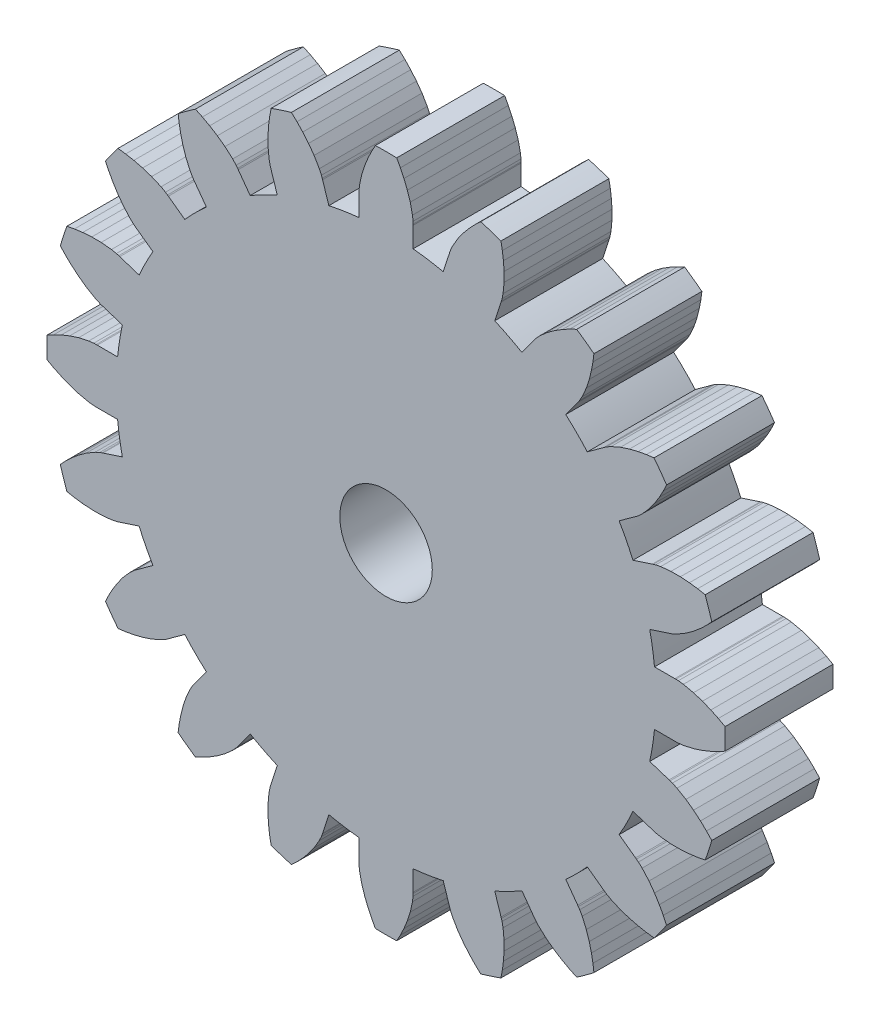
SolidWorks part; units mm, degrees
ref_plane "Front Plane" through (0, 0, 0) normal (0, 0, 1) x (1, 0, 0)
ref_plane "Top Plane" through (0, 0, 0) normal (0, 1, 0) x (1, 0, 0)
ref_plane "Right Plane" through (0, 0, 0) normal (1, 0, 0) x (0, 0, -1)
ref_plane "Plan1" through (0, 0, 10) normal (0, 0, 1) x (1, 0, 0)
sketch "Esquisse1" plane through (0, 0, 10) normal (0, 0, 1) x (1, 0, 0)
  line L0 (10.3919, 2.8876) -> (10.5632, 3.069)
  line L1 (10.3497, 3.726) -> (10.1045, 3.7722)
  line L2 (10.1045, 3.7722) -> (9.8372, 3.8071)
  line L3 (9.8372, 3.8071) -> (9.5442, 3.8279)
  line L4 (9.5442, 3.8279) -> (9.2385, 3.8276)
  line L5 (9.2385, 3.8276) -> (8.9055, 3.7951)
  line L6 (8.9055, 3.7951) -> (8.7443, 3.7625)
  line L7 (8.7443, 3.7625) -> (8.6676, 3.7409)
  line L8 (8.6676, 3.7409) -> (8.6349, 3.7295)
  line L9 (8.6349, 3.7295) -> (8.0083, 3.5256)
  line L10 (7.5594, 4.4066) -> (8.0927, 4.7936)
  line L11 (8.0927, 4.7936) -> (8.1211, 4.8134)
  line L12 (8.1211, 4.8134) -> (8.1837, 4.8627)
  line L13 (8.1837, 4.8627) -> (8.3048, 4.974)
  line L14 (8.3048, 4.974) -> (8.5268, 5.2243)
  line L15 (8.5268, 5.2243) -> (8.7068, 5.4714)
  line L16 (8.7068, 5.4714) -> (8.8622, 5.7207)
  line L17 (8.8622, 5.7207) -> (8.991, 5.9575)
  line L18 (8.991, 5.9575) -> (9.0978, 6.183)
  line L19 (8.6918, 6.7419) -> (8.4443, 6.71)
  line L20 (8.4443, 6.71) -> (8.1793, 6.6606)
  line L21 (8.1793, 6.6606) -> (7.8942, 6.5899)
  line L22 (7.8942, 6.5899) -> (7.6035, 6.4951)
  line L23 (7.6035, 6.4951) -> (7.2969, 6.3613)
  line L24 (7.2969, 6.3613) -> (7.1536, 6.2805)
  line L25 (7.1536, 6.2805) -> (7.0874, 6.2362)
  line L26 (7.0874, 6.2362) -> (7.0598, 6.2153)
  line L27 (7.0598, 6.2153) -> (6.5269, 5.8277)
  line L28 (5.8277, 6.5269) -> (6.2153, 7.0598)
  line L29 (6.2153, 7.0598) -> (6.2362, 7.0874)
  line L30 (6.2362, 7.0874) -> (6.2805, 7.1536)
  line L31 (6.2805, 7.1536) -> (6.3613, 7.2969)
  line L32 (6.3613, 7.2969) -> (6.4951, 7.6035)
  line L33 (6.4951, 7.6035) -> (6.5899, 7.8942)
  line L34 (6.5899, 7.8942) -> (6.6606, 8.1793)
  line L35 (6.6606, 8.1793) -> (6.71, 8.4443)
  line L36 (6.71, 8.4443) -> (6.7419, 8.6918)
  line L37 (6.183, 9.0978) -> (5.9575, 8.991)
  line L38 (5.9575, 8.991) -> (5.7207, 8.8622)
  line L39 (5.7207, 8.8622) -> (5.4714, 8.7068)
  line L40 (5.4714, 8.7068) -> (5.2243, 8.5268)
  line L41 (5.2243, 8.5268) -> (4.974, 8.3048)
  line L42 (4.974, 8.3048) -> (4.8627, 8.1837)
  line L43 (4.8627, 8.1837) -> (4.8134, 8.1211)
  line L44 (4.8134, 8.1211) -> (4.7936, 8.0927)
  line L45 (4.7936, 8.0927) -> (4.4066, 7.5594)
  line L46 (3.5256, 8.0083) -> (3.7295, 8.6349)
  line L47 (3.7295, 8.6349) -> (3.7409, 8.6676)
  line L48 (3.7409, 8.6676) -> (3.7625, 8.7443)
  line L49 (3.7625, 8.7443) -> (3.7951, 8.9055)
  line L50 (3.7951, 8.9055) -> (3.8276, 9.2385)
  line L51 (3.8276, 9.2385) -> (3.8279, 9.5442)
  line L52 (3.8279, 9.5442) -> (3.8071, 9.8372)
  line L53 (3.8071, 9.8372) -> (3.7722, 10.1045)
  line L54 (3.7722, 10.1045) -> (3.726, 10.3497)
  line L55 (3.069, 10.5632) -> (2.8876, 10.3919)
  line L56 (2.8876, 10.3919) -> (2.7022, 10.1962)
  line L57 (2.7022, 10.1962) -> (2.5131, 9.9714)
  line L58 (2.5131, 9.9714) -> (2.3337, 9.7239)
  line L59 (2.3337, 9.7239) -> (2.1642, 9.4354)
  line L60 (2.1642, 9.4354) -> (2.0958, 9.2858)
  line L61 (2.0958, 9.2858) -> (2.0682, 9.211)
  line L62 (2.0682, 9.211) -> (2.0582, 9.1779)
  line L63 (2.0582, 9.1779) -> (1.8549, 8.5511)
  line L64 (0.8783, 8.7058) -> (0.8787, 9.3647)
  line L65 (0.8787, 9.3647) -> (0.8794, 9.3993)
  line L66 (0.8794, 9.3993) -> (0.8763, 9.479)
  line L67 (0.8763, 9.479) -> (0.8574, 9.6424)
  line L68 (0.8574, 9.6424) -> (0.7854, 9.9691)
  line L69 (0.7854, 9.9691) -> (0.6913, 10.26)
  line L70 (0.6913, 10.26) -> (0.5809, 10.5322)
  line L71 (0.5809, 10.5322) -> (0.4651, 10.7756)
  line L72 (0.4651, 10.7756) -> (0.3454, 10.9946)
  line L73 (-0.3454, 10.9946) -> (-0.4651, 10.7756)
  line L74 (-0.4651, 10.7756) -> (-0.5809, 10.5322)
  line L75 (-0.5809, 10.5322) -> (-0.6913, 10.26)
  line L76 (-0.6913, 10.26) -> (-0.7854, 9.9691)
  line L77 (-0.7854, 9.9691) -> (-0.8574, 9.6424)
  line L78 (-0.8574, 9.6424) -> (-0.8763, 9.479)
  line L79 (-0.8763, 9.479) -> (-0.8794, 9.3993)
  line L80 (-0.8794, 9.3993) -> (-0.8787, 9.3647)
  line L81 (-0.8787, 9.3647) -> (-0.8783, 8.7058)
  line L82 (-1.8549, 8.5511) -> (-2.0582, 9.1779)
  line L83 (-2.0582, 9.1779) -> (-2.0682, 9.211)
  line L84 (-2.0682, 9.211) -> (-2.0958, 9.2858)
  line L85 (-2.0958, 9.2858) -> (-2.1642, 9.4354)
  line L86 (-2.1642, 9.4354) -> (-2.3337, 9.7239)
  line L87 (-2.3337, 9.7239) -> (-2.5131, 9.9714)
  line L88 (-2.5131, 9.9714) -> (-2.7022, 10.1962)
  line L89 (-2.7022, 10.1962) -> (-2.8876, 10.3919)
  line L90 (-2.8876, 10.3919) -> (-3.069, 10.5632)
  line L91 (-3.726, 10.3497) -> (-3.7722, 10.1045)
  line L92 (-3.7722, 10.1045) -> (-3.8071, 9.8372)
  line L93 (-3.8071, 9.8372) -> (-3.8279, 9.5442)
  line L94 (-3.8279, 9.5442) -> (-3.8276, 9.2385)
  line L95 (-3.8276, 9.2385) -> (-3.7951, 8.9055)
  line L96 (-3.7951, 8.9055) -> (-3.7625, 8.7443)
  line L97 (-3.7625, 8.7443) -> (-3.7409, 8.6676)
  line L98 (-3.7409, 8.6676) -> (-3.7295, 8.6349)
  line L99 (-3.7295, 8.6349) -> (-3.5256, 8.0083)
  line L100 (-4.4066, 7.5594) -> (-4.7936, 8.0927)
  line L101 (-4.7936, 8.0927) -> (-4.8134, 8.1211)
  line L102 (-4.8134, 8.1211) -> (-4.8627, 8.1837)
  line L103 (-4.8627, 8.1837) -> (-4.974, 8.3048)
  line L104 (-4.974, 8.3048) -> (-5.2243, 8.5268)
  line L105 (-5.2243, 8.5268) -> (-5.4714, 8.7068)
  line L106 (-5.4714, 8.7068) -> (-5.7207, 8.8622)
  line L107 (-5.7207, 8.8622) -> (-5.9575, 8.991)
  line L108 (-5.9575, 8.991) -> (-6.183, 9.0978)
  line L109 (-6.7419, 8.6918) -> (-6.71, 8.4443)
  line L110 (-6.71, 8.4443) -> (-6.6606, 8.1793)
  line L111 (-6.6606, 8.1793) -> (-6.5899, 7.8942)
  line L112 (-6.5899, 7.8942) -> (-6.4951, 7.6035)
  line L113 (-6.4951, 7.6035) -> (-6.3613, 7.2969)
  line L114 (-6.3613, 7.2969) -> (-6.2805, 7.1536)
  line L115 (-6.2805, 7.1536) -> (-6.2362, 7.0874)
  line L116 (-6.2362, 7.0874) -> (-6.2153, 7.0598)
  line L117 (-6.2153, 7.0598) -> (-5.8277, 6.5269)
  line L118 (-6.5269, 5.8277) -> (-7.0598, 6.2153)
  line L119 (-7.0598, 6.2153) -> (-7.0874, 6.2362)
  line L120 (-7.0874, 6.2362) -> (-7.1536, 6.2805)
  line L121 (-7.1536, 6.2805) -> (-7.2969, 6.3613)
  line L122 (-7.2969, 6.3613) -> (-7.6035, 6.4951)
  line L123 (-7.6035, 6.4951) -> (-7.8942, 6.5899)
  line L124 (-7.8942, 6.5899) -> (-8.1793, 6.6606)
  line L125 (-8.1793, 6.6606) -> (-8.4443, 6.71)
  line L126 (-8.4443, 6.71) -> (-8.6918, 6.7419)
  line L127 (-9.0978, 6.183) -> (-8.991, 5.9575)
  line L128 (-8.991, 5.9575) -> (-8.8622, 5.7207)
  line L129 (-8.8622, 5.7207) -> (-8.7068, 5.4714)
  line L130 (-8.7068, 5.4714) -> (-8.5268, 5.2243)
  line L131 (-8.5268, 5.2243) -> (-8.3048, 4.974)
  line L132 (-8.3048, 4.974) -> (-8.1837, 4.8627)
  line L133 (-8.1837, 4.8627) -> (-8.1211, 4.8134)
  line L134 (-8.1211, 4.8134) -> (-8.0927, 4.7936)
  line L135 (-8.0927, 4.7936) -> (-7.5594, 4.4066)
  line L136 (-8.0083, 3.5256) -> (-8.6349, 3.7295)
  line L137 (-8.6349, 3.7295) -> (-8.6676, 3.7409)
  line L138 (-8.6676, 3.7409) -> (-8.7443, 3.7625)
  line L139 (-8.7443, 3.7625) -> (-8.9055, 3.7951)
  line L140 (-8.9055, 3.7951) -> (-9.2385, 3.8276)
  line L141 (-9.2385, 3.8276) -> (-9.5442, 3.8279)
  line L142 (-9.5442, 3.8279) -> (-9.8372, 3.8071)
  line L143 (-9.8372, 3.8071) -> (-10.1045, 3.7722)
  line L144 (-10.1045, 3.7722) -> (-10.3497, 3.726)
  line L145 (-10.5632, 3.069) -> (-10.3919, 2.8876)
  line L146 (-10.3919, 2.8876) -> (-10.1962, 2.7022)
  line L147 (-10.1962, 2.7022) -> (-9.9714, 2.5131)
  line L148 (-9.9714, 2.5131) -> (-9.7239, 2.3337)
  line L149 (-9.7239, 2.3337) -> (-9.4354, 2.1642)
  line L150 (-9.4354, 2.1642) -> (-9.2858, 2.0958)
  line L151 (-9.2858, 2.0958) -> (-9.211, 2.0682)
  line L152 (-9.211, 2.0682) -> (-9.1779, 2.0582)
  line L153 (-9.1779, 2.0582) -> (-8.5511, 1.8549)
  line L154 (-8.7058, 0.8783) -> (-9.3647, 0.8787)
  line L155 (-9.3647, 0.8787) -> (-9.3993, 0.8794)
  line L156 (-9.3993, 0.8794) -> (-9.479, 0.8763)
  line L157 (-9.479, 0.8763) -> (-9.6424, 0.8574)
  line L158 (-9.6424, 0.8574) -> (-9.9691, 0.7854)
  line L159 (-9.9691, 0.7854) -> (-10.26, 0.6913)
  line L160 (-10.26, 0.6913) -> (-10.5322, 0.5809)
  line L161 (-10.5322, 0.5809) -> (-10.7756, 0.4651)
  line L162 (-10.7756, 0.4651) -> (-10.9946, 0.3454)
  line L163 (-10.9946, -0.3454) -> (-10.7756, -0.4651)
  line L164 (-10.7756, -0.4651) -> (-10.5322, -0.5809)
  line L165 (-10.5322, -0.5809) -> (-10.26, -0.6913)
  line L166 (-10.26, -0.6913) -> (-9.9691, -0.7854)
  line L167 (-9.9691, -0.7854) -> (-9.6424, -0.8574)
  line L168 (-9.6424, -0.8574) -> (-9.479, -0.8763)
  line L169 (-9.479, -0.8763) -> (-9.3993, -0.8794)
  line L170 (-9.3993, -0.8794) -> (-9.3647, -0.8787)
  line L171 (-9.3647, -0.8787) -> (-8.7058, -0.8783)
  line L172 (-8.5511, -1.8549) -> (-9.1779, -2.0582)
  line L173 (-9.1779, -2.0582) -> (-9.211, -2.0682)
  line L174 (-9.211, -2.0682) -> (-9.2858, -2.0958)
  line L175 (-9.2858, -2.0958) -> (-9.4354, -2.1642)
  line L176 (-9.4354, -2.1642) -> (-9.7239, -2.3337)
  line L177 (-9.7239, -2.3337) -> (-9.9714, -2.5131)
  line L178 (-9.9714, -2.5131) -> (-10.1962, -2.7022)
  line L179 (-10.1962, -2.7022) -> (-10.3919, -2.8876)
  line L180 (-10.3919, -2.8876) -> (-10.5632, -3.069)
  line L181 (-10.3497, -3.726) -> (-10.1045, -3.7722)
  line L182 (-10.1045, -3.7722) -> (-9.8372, -3.8071)
  line L183 (-9.8372, -3.8071) -> (-9.5442, -3.8279)
  line L184 (-9.5442, -3.8279) -> (-9.2385, -3.8276)
  line L185 (-9.2385, -3.8276) -> (-8.9055, -3.7951)
  line L186 (-8.9055, -3.7951) -> (-8.7443, -3.7625)
  line L187 (-8.7443, -3.7625) -> (-8.6676, -3.7409)
  line L188 (-8.6676, -3.7409) -> (-8.6349, -3.7295)
  line L189 (-8.6349, -3.7295) -> (-8.0083, -3.5256)
  line L190 (-7.5594, -4.4066) -> (-8.0927, -4.7936)
  line L191 (-8.0927, -4.7936) -> (-8.1211, -4.8134)
  line L192 (-8.1211, -4.8134) -> (-8.1837, -4.8627)
  line L193 (-8.1837, -4.8627) -> (-8.3048, -4.974)
  line L194 (-8.3048, -4.974) -> (-8.5268, -5.2243)
  line L195 (-8.5268, -5.2243) -> (-8.7068, -5.4714)
  line L196 (-8.7068, -5.4714) -> (-8.8622, -5.7207)
  line L197 (-8.8622, -5.7207) -> (-8.991, -5.9575)
  line L198 (-8.991, -5.9575) -> (-9.0978, -6.183)
  line L199 (-8.6918, -6.7419) -> (-8.4443, -6.71)
  line L200 (-8.4443, -6.71) -> (-8.1793, -6.6606)
  line L201 (-8.1793, -6.6606) -> (-7.8942, -6.5899)
  line L202 (-7.8942, -6.5899) -> (-7.6035, -6.4951)
  line L203 (-7.6035, -6.4951) -> (-7.2969, -6.3613)
  line L204 (-7.2969, -6.3613) -> (-7.1536, -6.2805)
  line L205 (-7.1536, -6.2805) -> (-7.0874, -6.2362)
  line L206 (-7.0874, -6.2362) -> (-7.0598, -6.2153)
  line L207 (-7.0598, -6.2153) -> (-6.5269, -5.8277)
  line L208 (-5.8277, -6.5269) -> (-6.2153, -7.0598)
  line L209 (-6.2153, -7.0598) -> (-6.2362, -7.0874)
  line L210 (-6.2362, -7.0874) -> (-6.2805, -7.1536)
  line L211 (-6.2805, -7.1536) -> (-6.3613, -7.2969)
  line L212 (-6.3613, -7.2969) -> (-6.4951, -7.6035)
  line L213 (-6.4951, -7.6035) -> (-6.5899, -7.8942)
  line L214 (-6.5899, -7.8942) -> (-6.6606, -8.1793)
  line L215 (-6.6606, -8.1793) -> (-6.71, -8.4443)
  line L216 (-6.71, -8.4443) -> (-6.7419, -8.6918)
  line L217 (-6.183, -9.0978) -> (-5.9575, -8.991)
  line L218 (-5.9575, -8.991) -> (-5.7207, -8.8622)
  line L219 (-5.7207, -8.8622) -> (-5.4714, -8.7068)
  line L220 (-5.4714, -8.7068) -> (-5.2243, -8.5268)
  line L221 (-5.2243, -8.5268) -> (-4.974, -8.3048)
  line L222 (-4.974, -8.3048) -> (-4.8627, -8.1837)
  line L223 (-4.8627, -8.1837) -> (-4.8134, -8.1211)
  line L224 (-4.8134, -8.1211) -> (-4.7936, -8.0927)
  line L225 (-4.7936, -8.0927) -> (-4.4066, -7.5594)
  line L226 (-3.5256, -8.0083) -> (-3.7295, -8.6349)
  line L227 (-3.7295, -8.6349) -> (-3.7409, -8.6676)
  line L228 (-3.7409, -8.6676) -> (-3.7625, -8.7443)
  line L229 (-3.7625, -8.7443) -> (-3.7951, -8.9055)
  line L230 (-3.7951, -8.9055) -> (-3.8276, -9.2385)
  line L231 (-3.8276, -9.2385) -> (-3.8279, -9.5442)
  line L232 (-3.8279, -9.5442) -> (-3.8071, -9.8372)
  line L233 (-3.8071, -9.8372) -> (-3.7722, -10.1045)
  line L234 (-3.7722, -10.1045) -> (-3.726, -10.3497)
  line L235 (-3.069, -10.5632) -> (-2.8876, -10.3919)
  line L236 (-2.8876, -10.3919) -> (-2.7022, -10.1962)
  line L237 (-2.7022, -10.1962) -> (-2.5131, -9.9714)
  line L238 (-2.5131, -9.9714) -> (-2.3337, -9.7239)
  line L239 (-2.3337, -9.7239) -> (-2.1642, -9.4354)
  line L240 (-2.1642, -9.4354) -> (-2.0958, -9.2858)
  line L241 (-2.0958, -9.2858) -> (-2.0682, -9.211)
  line L242 (-2.0682, -9.211) -> (-2.0582, -9.1779)
  line L243 (-2.0582, -9.1779) -> (-1.8549, -8.5511)
  line L244 (-0.8783, -8.7058) -> (-0.8787, -9.3647)
  line L245 (-0.8787, -9.3647) -> (-0.8794, -9.3993)
  line L246 (-0.8794, -9.3993) -> (-0.8763, -9.479)
  line L247 (-0.8763, -9.479) -> (-0.8574, -9.6424)
  line L248 (-0.8574, -9.6424) -> (-0.7854, -9.9691)
  line L249 (-0.7854, -9.9691) -> (-0.6913, -10.26)
  line L250 (-0.6913, -10.26) -> (-0.5809, -10.5322)
  line L251 (-0.5809, -10.5322) -> (-0.4651, -10.7756)
  line L252 (-0.4651, -10.7756) -> (-0.3454, -10.9946)
  line L253 (0.3454, -10.9946) -> (0.4651, -10.7756)
  line L254 (0.4651, -10.7756) -> (0.5809, -10.5322)
  line L255 (0.5809, -10.5322) -> (0.6913, -10.26)
  line L256 (0.6913, -10.26) -> (0.7854, -9.9691)
  line L257 (0.7854, -9.9691) -> (0.8574, -9.6424)
  line L258 (0.8574, -9.6424) -> (0.8763, -9.479)
  line L259 (0.8763, -9.479) -> (0.8794, -9.3993)
  line L260 (0.8794, -9.3993) -> (0.8787, -9.3647)
  line L261 (0.8787, -9.3647) -> (0.8783, -8.7058)
  line L262 (1.8549, -8.5511) -> (2.0582, -9.1779)
  line L263 (2.0582, -9.1779) -> (2.0682, -9.211)
  line L264 (2.0682, -9.211) -> (2.0958, -9.2858)
  line L265 (2.0958, -9.2858) -> (2.1642, -9.4354)
  line L266 (2.1642, -9.4354) -> (2.3337, -9.7239)
  line L267 (2.3337, -9.7239) -> (2.5131, -9.9714)
  line L268 (2.5131, -9.9714) -> (2.7022, -10.1962)
  line L269 (2.7022, -10.1962) -> (2.8876, -10.3919)
  line L270 (2.8876, -10.3919) -> (3.069, -10.5632)
  line L271 (3.726, -10.3497) -> (3.7722, -10.1045)
  line L272 (3.7722, -10.1045) -> (3.8071, -9.8372)
  line L273 (3.8071, -9.8372) -> (3.8279, -9.5442)
  line L274 (3.8279, -9.5442) -> (3.8276, -9.2385)
  line L275 (3.8276, -9.2385) -> (3.7951, -8.9055)
  line L276 (3.7951, -8.9055) -> (3.7625, -8.7443)
  line L277 (3.7625, -8.7443) -> (3.7409, -8.6676)
  line L278 (3.7409, -8.6676) -> (3.7295, -8.6349)
  line L279 (3.7295, -8.6349) -> (3.5256, -8.0083)
  line L280 (4.4066, -7.5594) -> (4.7936, -8.0927)
  line L281 (4.7936, -8.0927) -> (4.8134, -8.1211)
  line L282 (4.8134, -8.1211) -> (4.8627, -8.1837)
  line L283 (4.8627, -8.1837) -> (4.974, -8.3048)
  line L284 (4.974, -8.3048) -> (5.2243, -8.5268)
  line L285 (5.2243, -8.5268) -> (5.4714, -8.7068)
  line L286 (5.4714, -8.7068) -> (5.7207, -8.8622)
  line L287 (5.7207, -8.8622) -> (5.9575, -8.991)
  line L288 (5.9575, -8.991) -> (6.183, -9.0978)
  line L289 (6.7419, -8.6918) -> (6.71, -8.4443)
  line L290 (6.71, -8.4443) -> (6.6606, -8.1793)
  line L291 (6.6606, -8.1793) -> (6.5899, -7.8942)
  line L292 (6.5899, -7.8942) -> (6.4951, -7.6035)
  line L293 (6.4951, -7.6035) -> (6.3613, -7.2969)
  line L294 (6.3613, -7.2969) -> (6.2805, -7.1536)
  line L295 (6.2805, -7.1536) -> (6.2362, -7.0874)
  line L296 (6.2362, -7.0874) -> (6.2153, -7.0598)
  line L297 (6.2153, -7.0598) -> (5.8277, -6.5269)
  line L298 (6.5269, -5.8277) -> (7.0598, -6.2153)
  line L299 (7.0598, -6.2153) -> (7.0874, -6.2362)
  line L300 (7.0874, -6.2362) -> (7.1536, -6.2805)
  line L301 (7.1536, -6.2805) -> (7.2969, -6.3613)
  line L302 (7.2969, -6.3613) -> (7.6035, -6.4951)
  line L303 (7.6035, -6.4951) -> (7.8942, -6.5899)
  line L304 (7.8942, -6.5899) -> (8.1793, -6.6606)
  line L305 (8.1793, -6.6606) -> (8.4443, -6.71)
  line L306 (8.4443, -6.71) -> (8.6918, -6.7419)
  line L307 (9.0978, -6.183) -> (8.991, -5.9575)
  line L308 (8.991, -5.9575) -> (8.8622, -5.7207)
  line L309 (8.8622, -5.7207) -> (8.7068, -5.4714)
  line L310 (8.7068, -5.4714) -> (8.5268, -5.2243)
  line L311 (8.5268, -5.2243) -> (8.3048, -4.974)
  line L312 (8.3048, -4.974) -> (8.1837, -4.8627)
  line L313 (8.1837, -4.8627) -> (8.1211, -4.8134)
  line L314 (8.1211, -4.8134) -> (8.0927, -4.7936)
  line L315 (8.0927, -4.7936) -> (7.5594, -4.4066)
  line L316 (8.0083, -3.5256) -> (8.6349, -3.7295)
  line L317 (8.6349, -3.7295) -> (8.6676, -3.7409)
  line L318 (8.6676, -3.7409) -> (8.7443, -3.7625)
  line L319 (8.7443, -3.7625) -> (8.9055, -3.7951)
  line L320 (8.9055, -3.7951) -> (9.2385, -3.8276)
  line L321 (9.2385, -3.8276) -> (9.5442, -3.8279)
  line L322 (9.5442, -3.8279) -> (9.8372, -3.8071)
  line L323 (9.8372, -3.8071) -> (10.1045, -3.7722)
  line L324 (10.1045, -3.7722) -> (10.3497, -3.726)
  line L325 (10.5632, -3.069) -> (10.3919, -2.8876)
  line L326 (10.3919, -2.8876) -> (10.1962, -2.7022)
  line L327 (10.1962, -2.7022) -> (9.9714, -2.5131)
  line L328 (9.9714, -2.5131) -> (9.7239, -2.3337)
  line L329 (9.7239, -2.3337) -> (9.4354, -2.1642)
  line L330 (9.4354, -2.1642) -> (9.2858, -2.0958)
  line L331 (9.2858, -2.0958) -> (9.211, -2.0682)
  line L332 (9.211, -2.0682) -> (9.1779, -2.0582)
  line L333 (9.1779, -2.0582) -> (8.5511, -1.8549)
  line L334 (8.7058, -0.8783) -> (9.3647, -0.8787)
  line L335 (9.3647, -0.8787) -> (9.3993, -0.8794)
  line L336 (9.3993, -0.8794) -> (9.479, -0.8763)
  line L337 (9.479, -0.8763) -> (9.6424, -0.8574)
  line L338 (9.6424, -0.8574) -> (9.9691, -0.7854)
  line L339 (9.9691, -0.7854) -> (10.26, -0.6913)
  line L340 (10.26, -0.6913) -> (10.5322, -0.5809)
  line L341 (10.5322, -0.5809) -> (10.7756, -0.4651)
  line L342 (10.7756, -0.4651) -> (10.9946, -0.3454)
  line L343 (10.9946, 0.3454) -> (10.7756, 0.4651)
  line L344 (10.7756, 0.4651) -> (10.5322, 0.5809)
  line L345 (10.5322, 0.5809) -> (10.26, 0.6913)
  line L346 (10.26, 0.6913) -> (9.9691, 0.7854)
  line L347 (9.9691, 0.7854) -> (9.6424, 0.8574)
  line L348 (9.6424, 0.8574) -> (9.479, 0.8763)
  line L349 (9.479, 0.8763) -> (9.3993, 0.8794)
  line L350 (9.3993, 0.8794) -> (9.3647, 0.8787)
  line L351 (9.3647, 0.8787) -> (8.7058, 0.8783)
  line L352 (8.5511, 1.8549) -> (9.1779, 2.0582)
  line L353 (9.1779, 2.0582) -> (9.211, 2.0682)
  line L354 (9.211, 2.0682) -> (9.2858, 2.0958)
  line L355 (9.2858, 2.0958) -> (9.4354, 2.1642)
  line L356 (9.4354, 2.1642) -> (9.7239, 2.3337)
  line L357 (9.7239, 2.3337) -> (9.9714, 2.5131)
  line L358 (9.9714, 2.5131) -> (10.1962, 2.7022)
  line L359 (10.1962, 2.7022) -> (10.3919, 2.8876)
  arc A0 (10.5632, 3.069) -> (10.3497, 3.726) centre (0, 0) ccw
  arc A1 (8.0083, 3.5256) -> (7.5594, 4.4066) centre (0, 0) ccw
  arc A2 (9.0978, 6.183) -> (8.6918, 6.7419) centre (0, 0) ccw
  arc A3 (6.5269, 5.8277) -> (5.8277, 6.5269) centre (0, 0) ccw
  arc A4 (6.7419, 8.6918) -> (6.183, 9.0978) centre (0, 0) ccw
  arc A5 (4.4066, 7.5594) -> (3.5256, 8.0083) centre (0, 0) ccw
  arc A6 (3.726, 10.3497) -> (3.069, 10.5632) centre (0, 0) ccw
  arc A7 (1.8549, 8.5511) -> (0.8783, 8.7058) centre (0, 0) ccw
  arc A8 (0.3454, 10.9946) -> (-0.3454, 10.9946) centre (0, 0) ccw
  arc A9 (-0.8783, 8.7058) -> (-1.8549, 8.5511) centre (0, 0) ccw
  arc A10 (-3.069, 10.5632) -> (-3.726, 10.3497) centre (0, 0) ccw
  arc A11 (-3.5256, 8.0083) -> (-4.4066, 7.5594) centre (0, 0) ccw
  arc A12 (-6.183, 9.0978) -> (-6.7419, 8.6918) centre (0, 0) ccw
  arc A13 (-5.8277, 6.5269) -> (-6.5269, 5.8277) centre (0, 0) ccw
  arc A14 (-8.6918, 6.7419) -> (-9.0978, 6.183) centre (0, 0) ccw
  arc A15 (-7.5594, 4.4066) -> (-8.0083, 3.5256) centre (0, 0) ccw
  arc A16 (-10.3497, 3.726) -> (-10.5632, 3.069) centre (0, 0) ccw
  arc A17 (-8.5511, 1.8549) -> (-8.7058, 0.8783) centre (0, 0) ccw
  arc A18 (-10.9946, 0.3454) -> (-10.9946, -0.3454) centre (0, 0) ccw
  arc A19 (-8.7058, -0.8783) -> (-8.5511, -1.8549) centre (0, 0) ccw
  arc A20 (-10.5632, -3.069) -> (-10.3497, -3.726) centre (0, 0) ccw
  arc A21 (-8.0083, -3.5256) -> (-7.5594, -4.4066) centre (0, 0) ccw
  arc A22 (-9.0978, -6.183) -> (-8.6918, -6.7419) centre (0, 0) ccw
  arc A23 (-6.5269, -5.8277) -> (-5.8277, -6.5269) centre (0, 0) ccw
  arc A24 (-6.7419, -8.6918) -> (-6.183, -9.0978) centre (0, 0) ccw
  arc A25 (-4.4066, -7.5594) -> (-3.5256, -8.0083) centre (0, 0) ccw
  arc A26 (-3.726, -10.3497) -> (-3.069, -10.5632) centre (0, 0) ccw
  arc A27 (-1.8549, -8.5511) -> (-0.8783, -8.7058) centre (0, 0) ccw
  arc A28 (-0.3454, -10.9946) -> (0.3454, -10.9946) centre (0, 0) ccw
  arc A29 (0.8783, -8.7058) -> (1.8549, -8.5511) centre (0, 0) ccw
  arc A30 (3.069, -10.5632) -> (3.726, -10.3497) centre (0, 0) ccw
  arc A31 (3.5256, -8.0083) -> (4.4066, -7.5594) centre (0, 0) ccw
  arc A32 (6.183, -9.0978) -> (6.7419, -8.6918) centre (0, 0) ccw
  arc A33 (5.8277, -6.5269) -> (6.5269, -5.8277) centre (0, 0) ccw
  arc A34 (8.6918, -6.7419) -> (9.0978, -6.183) centre (0, 0) ccw
  arc A35 (7.5594, -4.4066) -> (8.0083, -3.5256) centre (0, 0) ccw
  arc A36 (10.3497, -3.726) -> (10.5632, -3.069) centre (0, 0) ccw
  arc A37 (8.5511, -1.8549) -> (8.7058, -0.8783) centre (0, 0) ccw
  arc A38 (10.9946, -0.3454) -> (10.9946, 0.3454) centre (0, 0) ccw
  arc A39 (8.7058, 0.8783) -> (8.5511, 1.8549) centre (0, 0) ccw
  circle A40 centre (0, 0) radius 1.5
extrude "Boss.-Extru.1" add sketch "Esquisse1" against normal blind 3.5
